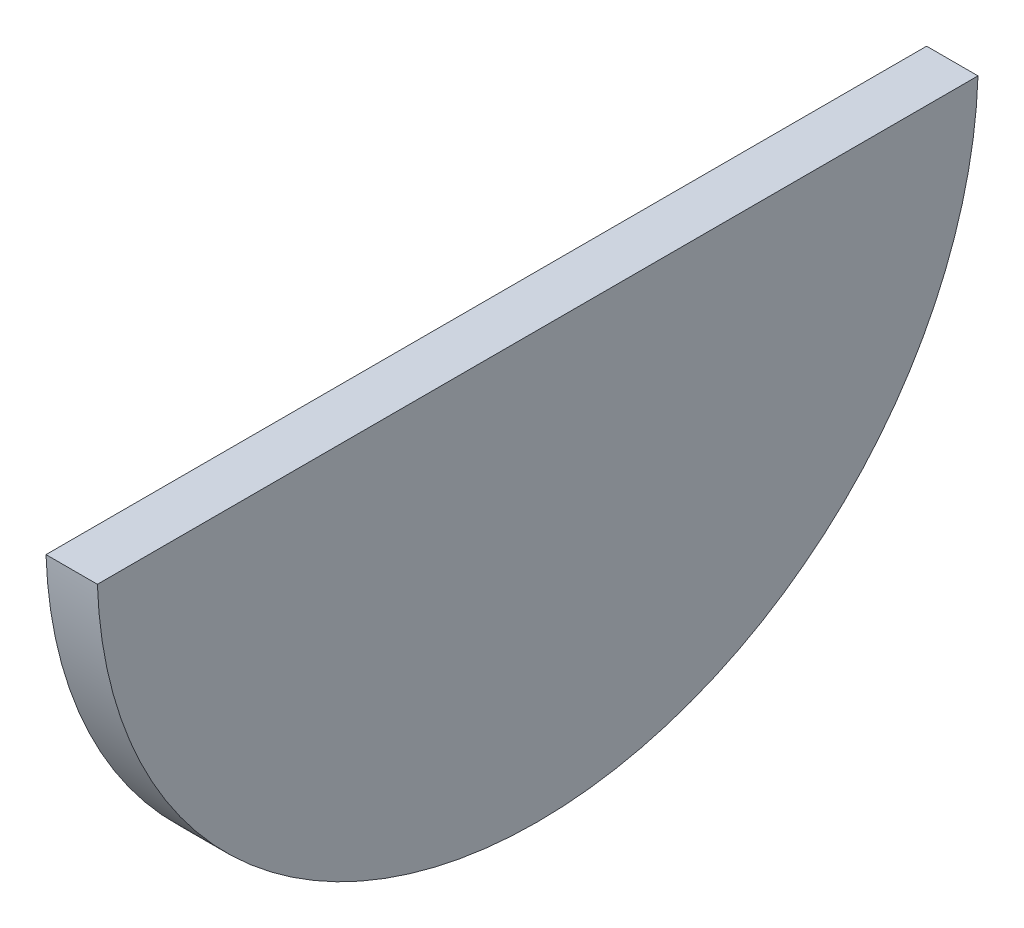
SolidWorks part; units mm, degrees
material "AISI 1020"
ref_plane "Front Plane" through (0, 0, 0) normal (0, 0, 1) x (1, 0, 0)
ref_plane "Top Plane" through (0, 0, 0) normal (0, 1, 0) x (1, 0, 0)
ref_plane "Right Plane" through (0, 0, 0) normal (1, 0, 0) x (0, 0, -1)
sketch "Sketch1" plane through (0, 0, 0) normal (1, 0, 0) x (0, 0, -1)
  line L0 (76.1577, 0) -> (-76.1577, 0)
  arc A0 (-76.1577, 0) -> (76.1577, 0) centre (0, 2.54) ccw
  dimension "D1" = 76.2
  dimension "D2" = 2.54
extrude "Boss-Extrude1" add sketch "Sketch1" along normal blind 8.89
